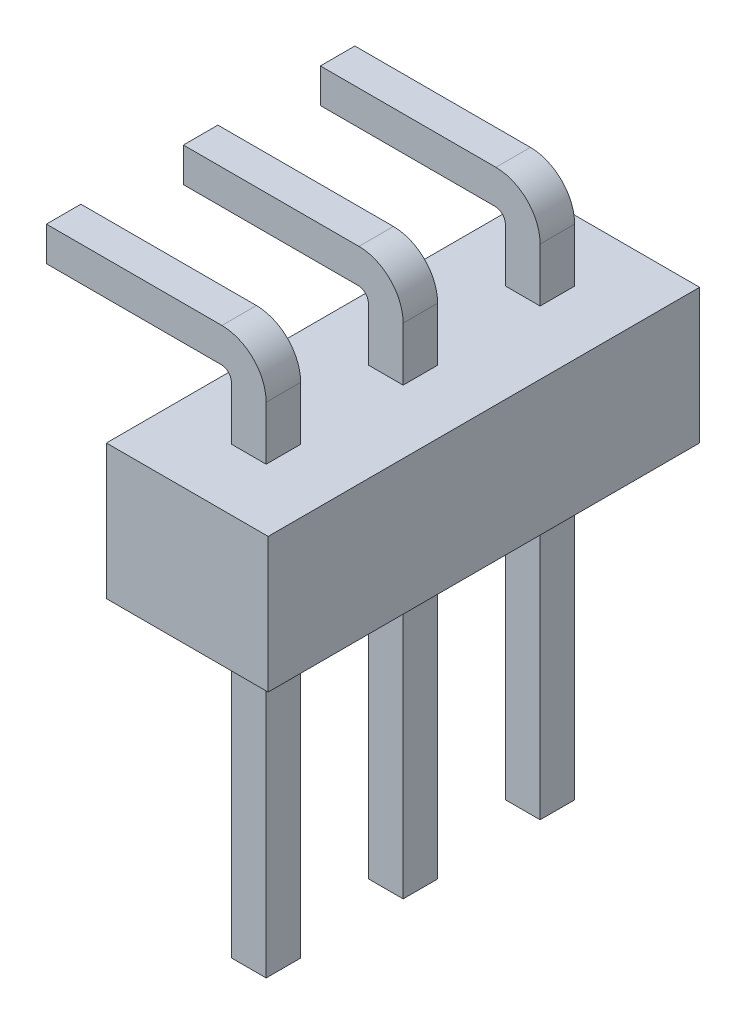
SolidWorks part; units mm, degrees
ref_plane "Front Plane" through (0, 0, 0) normal (0, 0, 1) x (1, 0, 0)
ref_plane "Top Plane" through (0, 0, 0) normal (0, 1, 0) x (1, 0, 0)
ref_plane "Right Plane" through (0, 0, 0) normal (1, 0, 0) x (0, 0, -1)
sketch "Sketch1" plane through (0, 0, 0) normal (0, 0, 1) x (1, 0, 0)
  line L0 (1.5, 0) -> (-1.5, 0) construction
  line L1 (-1.5, 1.25) -> (1.5, 1.25)
  line L2 (-1.5, 1.25) -> (-1.5, -1.25)
  line L3 (-1.5, -1.25) -> (1.5, -1.25)
  line L4 (1.5, 1.25) -> (1.5, -1.25)
  dimension "D1" = 3
  dimension "D2" = 2.5
extrude "Extrude1" add sketch "Sketch1" along normal mid plane 8
ref_plane "Plane4" through (0, 0, 2.86) normal (0, 0, 1) x (1, 0, 0)
sketch "Sketch2" plane through (0, 0, 2.86) normal (0, 0, 1) x (1, 0, 0)
  line L0 (-0.3225, 1.25) -> (-0.3225, 2.245)
  line L1 (1.5, 1.25) -> (-1.5, 1.25) construction
  line L2 (0.3225, 1.25) -> (0.3225, 2.245)
  line L3 (-0.3225, 1.25) -> (0.3225, 1.25)
  line L4 (0, 0) -> (0, 3.2035) construction
  line L5 (-0.5025, 2.4326) -> (-4.0025, 2.4326)
  line L6 (-4.0025, 2.4326) -> (-4.0025, 3.0683)
  line L7 (-4.0025, 3.0683) -> (-0.4975, 3.0683)
  line L8 (-0.3225, -1.25) -> (-0.3225, -7.25)
  line L9 (-1.5, -1.25) -> (1.5, -1.25) construction
  line L10 (-0.3225, -7.25) -> (0.3225, -7.25)
  line L11 (0.3225, -7.25) -> (0.3225, -1.25)
  line L12 (-0.3225, -1.25) -> (0.3225, -1.25)
  arc A0 (-0.3225, 2.245) -> (-0.5025, 2.4326) centre (-0.5103, 2.245) ccw
  arc A1 (0.3225, 2.245) -> (-0.4975, 3.0683) centre (-0.5008, 2.245) ccw
  dimension "D1" = 0.645
  dimension "D2" = 0.995
  dimension "D3" = 0.26
  dimension "D4" = 0.18
  dimension "D5" = 1.162
  dimension "D6" = 0.82
  dimension "D7" = 3.5
  dimension "D8" = 6
extrude "Extrude2" add sketch "Sketch2" against normal blind 0.64
pattern_linear "LPattern1" count 3 spacing 2.54 along (0, 0, -1) of "Extrude2"
chamfer "Chamfer1" distance 0.25 angle 45 24 edges at (-4.0025, 2.4326, 0) (-4.0025, 2.7505, -0.32) (-4.0025, 3.0683, 0) (-4.0025, 2.7505, 0.32) (0.3225, -7.25, 2.54) (0, -7.25, 2.22) (-0.3225, -7.25, 2.54) (0, -7.25, 2.86) (0.3225, -7.25, -2.54) (0, -7.25, -2.86) (-0.3225, -7.25, -2.54) (0, -7.25, -2.22) (0.3225, -7.25, 0) (0, -7.25, -0.32) (-0.3225, -7.25, 0) (0, -7.25, 0.32) (-4.0025, 2.4326, 2.54) (-4.0025, 2.7505, 2.22) (-4.0025, 3.0683, 2.54) (-4.0025, 2.7505, 2.86) (-4.0025, 2.4326, -2.54) (-4.0025, 2.7505, -2.86) (-4.0025, 3.0683, -2.54) (-4.0025, 2.7505, -2.22)
